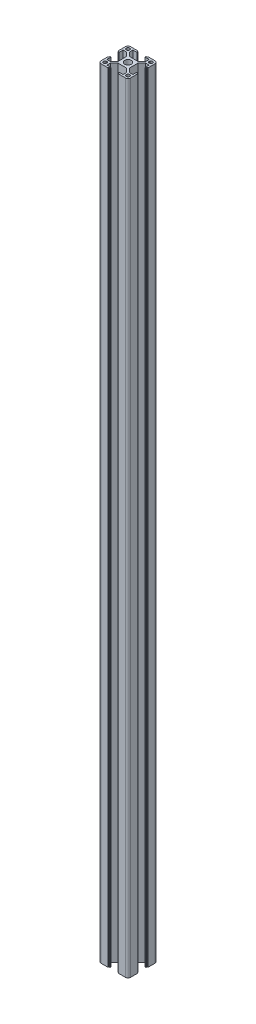
SolidWorks part; units mm, degrees
material "6063-T5"
ref_plane "前视基准面" through (0, 0, 0) normal (0, 0, 1) x (1, 0, 0)
ref_plane "上视基准面" through (0, 0, 0) normal (0, 1, 0) x (1, 0, 0)
ref_plane "右视基准面" through (0, 0, 0) normal (1, 0, 0) x (0, 0, -1)
sketch "草图3" plane through (0, 0, 0) normal (0, 1, 0) x (1, 0, 0)
  line L0 (0, 0) -> (-15, -15) construction
  line L1 (-15, -15) -> (-15, 0) construction
  line L2 (-15, 0) -> (0, 0) construction
  line L3 (-15, -12.5) -> (-15, -5.4)
  line L4 (-14.8, -5.2) -> (-14.4, -5.2)
  line L5 (-14.2, -5) -> (-14.2, -4.3)
  line L6 (-14, -4.1) -> (-13.2, -4.1)
  line L7 (-13.2, -4.1) -> (-13.2, -8.25)
  line L8 (-13.2, -8.25) -> (-9.5228, -8.25)
  line L9 (-9.5228, -8.25) -> (-5.8, -4.5272)
  line L10 (-5.8, -4.5272) -> (-5.8, 4.5272)
  line L11 (-13.2, -12.2) -> (-13.2, -11.05)
  line L12 (-12.2, -10.05) -> (-11.05, -10.05)
  line L13 (-4.5272, -5.8) -> (4.5272, -5.8)
  line L14 (-8.25, -9.5228) -> (-4.5272, -5.8)
  line L15 (-12.2, -13.2) -> (-11.05, -13.2)
  line L16 (-10.05, -12.2) -> (-10.05, -11.05)
  line L17 (-5.2, -14.8) -> (-5.2, -14.4)
  line L18 (-5, -14.2) -> (-4.3, -14.2)
  line L19 (-4.1, -14) -> (-4.1, -13.2)
  line L20 (-4.1, -13.2) -> (-8.25, -13.2)
  line L21 (-8.25, -13.2) -> (-8.25, -9.5228)
  line L22 (-12.5, -15) -> (-5.4, -15)
  line L23 (-12.5, 15) -> (-5.4, 15)
  line L24 (-8.25, 13.2) -> (-8.25, 9.5228)
  line L25 (-4.1, 13.2) -> (-8.25, 13.2)
  line L26 (-4.1, 14) -> (-4.1, 13.2)
  line L27 (-5, 14.2) -> (-4.3, 14.2)
  line L28 (-5.2, 14.8) -> (-5.2, 14.4)
  line L29 (-10.05, 12.2) -> (-10.05, 11.05)
  line L30 (-12.2, 13.2) -> (-11.05, 13.2)
  line L31 (-8.25, 9.5228) -> (-4.5272, 5.8)
  line L32 (-4.5272, 5.8) -> (4.5272, 5.8)
  line L33 (-12.2, 10.05) -> (-11.05, 10.05)
  line L34 (-13.2, 12.2) -> (-13.2, 11.05)
  line L35 (-9.5228, 8.25) -> (-5.8, 4.5272)
  line L36 (-13.2, 8.25) -> (-9.5228, 8.25)
  line L37 (-13.2, 4.1) -> (-13.2, 8.25)
  line L38 (-14, 4.1) -> (-13.2, 4.1)
  line L39 (-14.2, 5) -> (-14.2, 4.3)
  line L40 (-14.8, 5.2) -> (-14.4, 5.2)
  line L41 (-15, 12.5) -> (-15, 5.4)
  line L42 (0, 0) -> (0, -12.3268) construction
  line L43 (15, 12.5) -> (15, 5.4)
  line L44 (14.8, 5.2) -> (14.4, 5.2)
  line L45 (14.2, 5) -> (14.2, 4.3)
  line L46 (14, 4.1) -> (13.2, 4.1)
  line L47 (13.2, 4.1) -> (13.2, 8.25)
  line L48 (13.2, 8.25) -> (9.5228, 8.25)
  line L49 (9.5228, 8.25) -> (5.8, 4.5272)
  line L50 (13.2, 12.2) -> (13.2, 11.05)
  line L51 (12.2, 10.05) -> (11.05, 10.05)
  line L52 (8.25, 9.5228) -> (4.5272, 5.8)
  line L53 (12.2, 13.2) -> (11.05, 13.2)
  line L54 (10.05, 12.2) -> (10.05, 11.05)
  line L55 (5.2, 14.8) -> (5.2, 14.4)
  line L56 (5, 14.2) -> (4.3, 14.2)
  line L57 (4.1, 14) -> (4.1, 13.2)
  line L58 (4.1, 13.2) -> (8.25, 13.2)
  line L59 (8.25, 13.2) -> (8.25, 9.5228)
  line L60 (12.5, 15) -> (5.4, 15)
  line L61 (12.5, -15) -> (5.4, -15)
  line L62 (8.25, -13.2) -> (8.25, -9.5228)
  line L63 (4.1, -13.2) -> (8.25, -13.2)
  line L64 (4.1, -14) -> (4.1, -13.2)
  line L65 (5, -14.2) -> (4.3, -14.2)
  line L66 (5.2, -14.8) -> (5.2, -14.4)
  line L67 (10.05, -12.2) -> (10.05, -11.05)
  line L68 (12.2, -13.2) -> (11.05, -13.2)
  line L69 (8.25, -9.5228) -> (4.5272, -5.8)
  line L70 (12.2, -10.05) -> (11.05, -10.05)
  line L71 (13.2, -12.2) -> (13.2, -11.05)
  line L72 (5.8, -4.5272) -> (5.8, 4.5272)
  line L73 (9.5228, -8.25) -> (5.8, -4.5272)
  line L74 (13.2, -8.25) -> (9.5228, -8.25)
  line L75 (13.2, -4.1) -> (13.2, -8.25)
  line L76 (14, -4.1) -> (13.2, -4.1)
  line L77 (14.2, -5) -> (14.2, -4.3)
  line L78 (14.8, -5.2) -> (14.4, -5.2)
  line L79 (15, -12.5) -> (15, -5.4)
  circle A0 centre (0, 0) radius 3.4
  arc A1 (-12.5, 15) -> (-15, 12.5) centre (-12.5, 12.5) ccw
  arc A2 (15, 12.5) -> (12.5, 15) centre (12.5, 12.5) ccw
  arc A3 (12.5, -15) -> (15, -12.5) centre (12.5, -12.5) ccw
  arc A4 (-15, -12.5) -> (-12.5, -15) centre (-12.5, -12.5) ccw
  arc A5 (-12.2, 13.2) -> (-13.2, 12.2) centre (-12.2, 12.2) ccw
  arc A6 (-12.2, 10.05) -> (-13.2, 11.05) centre (-12.2, 11.05) cw
  arc A7 (-10.05, 11.05) -> (-11.05, 10.05) centre (-11.05, 11.05) cw
  arc A8 (-10.05, 12.2) -> (-11.05, 13.2) centre (-11.05, 12.2) ccw
  arc A9 (11.05, 10.05) -> (10.05, 11.05) centre (11.05, 11.05) cw
  arc A10 (11.05, 13.2) -> (10.05, 12.2) centre (11.05, 12.2) ccw
  arc A11 (13.2, 12.2) -> (12.2, 13.2) centre (12.2, 12.2) ccw
  arc A12 (13.2, 11.05) -> (12.2, 10.05) centre (12.2, 11.05) cw
  arc A13 (12.2, -10.05) -> (13.2, -11.05) centre (12.2, -11.05) cw
  arc A14 (10.05, -11.05) -> (11.05, -10.05) centre (11.05, -11.05) cw
  arc A15 (10.05, -12.2) -> (11.05, -13.2) centre (11.05, -12.2) ccw
  arc A16 (12.2, -13.2) -> (13.2, -12.2) centre (12.2, -12.2) ccw
  arc A17 (-13.2, -11.05) -> (-12.2, -10.05) centre (-12.2, -11.05) cw
  arc A18 (-11.05, -10.05) -> (-10.05, -11.05) centre (-11.05, -11.05) cw
  arc A19 (-11.05, -13.2) -> (-10.05, -12.2) centre (-11.05, -12.2) ccw
  arc A20 (-13.2, -12.2) -> (-12.2, -13.2) centre (-12.2, -12.2) ccw
  arc A21 (-15, -5.4) -> (-14.8, -5.2) centre (-14.8, -5.4) cw
  arc A22 (-14.4, -5.2) -> (-14.2, -5) centre (-14.4, -5) ccw
  arc A23 (-14.2, -4.3) -> (-14, -4.1) centre (-14, -4.3) cw
  arc A24 (-14, 4.1) -> (-14.2, 4.3) centre (-14, 4.3) cw
  arc A25 (-14.2, 5) -> (-14.4, 5.2) centre (-14.4, 5) ccw
  arc A26 (-14.8, 5.2) -> (-15, 5.4) centre (-14.8, 5.4) cw
  arc A27 (-5.4, 15) -> (-5.2, 14.8) centre (-5.4, 14.8) cw
  arc A28 (-5, 14.2) -> (-5.2, 14.4) centre (-5, 14.4) cw
  arc A29 (-4.1, 14) -> (-4.3, 14.2) centre (-4.3, 14) ccw
  arc A30 (5.2, 14.8) -> (5.4, 15) centre (5.4, 14.8) cw
  arc A31 (5.2, 14.4) -> (5, 14.2) centre (5, 14.4) cw
  arc A32 (4.3, 14.2) -> (4.1, 14) centre (4.3, 14) ccw
  arc A33 (15, 5.4) -> (14.8, 5.2) centre (14.8, 5.4) cw
  arc A34 (14.4, 5.2) -> (14.2, 5) centre (14.4, 5) ccw
  arc A35 (14.2, 4.3) -> (14, 4.1) centre (14, 4.3) cw
  arc A36 (14, -4.1) -> (14.2, -4.3) centre (14, -4.3) cw
  arc A37 (14.2, -5) -> (14.4, -5.2) centre (14.4, -5) ccw
  arc A38 (14.8, -5.2) -> (15, -5.4) centre (14.8, -5.4) cw
  arc A39 (5.4, -15) -> (5.2, -14.8) centre (5.4, -14.8) cw
  arc A40 (5, -14.2) -> (5.2, -14.4) centre (5, -14.4) cw
  arc A41 (4.1, -14) -> (4.3, -14.2) centre (4.3, -14) ccw
  arc A42 (-5.2, -14.4) -> (-5, -14.2) centre (-5, -14.4) cw
  arc A43 (-4.3, -14.2) -> (-4.1, -14) centre (-4.3, -14) ccw
  arc A44 (-5.2, -14.8) -> (-5.4, -15) centre (-5.4, -14.8) cw
  point P38 (-5.8, 0)
  point P46 (0, 5.8)
  point P47 (0, -5.8)
  point P83 (5.8, 0)
  point P87 (-15, 15)
  point P90 (15, 15)
  point P93 (15, -15)
  point P99 (-13.2, 13.2)
  point P102 (-13.2, 10.05)
  point P105 (-10.05, 10.05)
  point P108 (-10.05, 13.2)
  point P111 (10.05, 10.05)
  point P114 (10.05, 13.2)
  point P117 (13.2, 13.2)
  point P120 (13.2, 10.05)
  point P123 (13.2, -10.05)
  point P126 (10.05, -10.05)
  point P129 (10.05, -13.2)
  point P132 (13.2, -13.2)
  point P135 (-13.2, -10.05)
  point P138 (-10.05, -10.05)
  point P141 (-10.05, -13.2)
  point P144 (-13.2, -13.2)
  point P147 (-15, -5.2)
  point P150 (-14.2, -5.2)
  point P153 (-14.2, -4.1)
  point P156 (-14.2, 4.1)
  point P159 (-14.2, 5.2)
  point P162 (-15, 5.2)
  point P165 (-5.2, 15)
  point P168 (-5.2, 14.2)
  point P171 (-4.1, 14.2)
  point P174 (5.2, 15)
  point P177 (5.2, 14.2)
  point P180 (4.1, 14.2)
  point P183 (15, 5.2)
  point P186 (14.2, 5.2)
  point P189 (14.2, 4.1)
  point P192 (14.2, -4.1)
  point P195 (14.2, -5.2)
  point P198 (15, -5.2)
  point P201 (5.2, -15)
  point P204 (5.2, -14.2)
  point P207 (4.1, -14.2)
  point P210 (-5.2, -14.2)
  point P213 (-4.1, -14.2)
  point P216 (-5.2, -15)
  dimension "D11" = 6.8
  dimension "D12" = 2.5
  dimension "D13" = 1
  dimension "D14" = 0.2
  dimension "D2" = 15
  dimension "D3" = 4.1
  dimension "D4" = 5.2
  dimension "D5" = 0.8
  dimension "D6" = 1.8
  dimension "D7" = 9.2
  dimension "D8" = 8.25
  dimension "D9" = 0.9
  dimension "D10" = 1.8
extrude "凸台-拉伸1" add sketch "草图3" along normal blind 789
ref_plane "基准面1" through (-10.05, 394.5, 12.2) normal (0, -1, 0) x (-1, 0, 0)
sketch "草图4" plane through (0, 0, 5.8) normal (0, 0, 1) x (1, 0, 0)
  line L1 (-4.5272, 789) -> (4.5272, 789) construction
  line L2 (5.4, 0) -> (12.5, 0) construction
  circle A1 centre (0, 609) radius 3
  circle A2 centre (0, 180) radius 3
  circle A4 centre (0, 394.5) radius 3
  point P2 (0, 386.1803)
  dimension "D1" = 6
  dimension "D2" = 6
  dimension "D3" = 6
  dimension "D4" = 180
  dimension "D5" = 180
  dimension "D6" = 394.5
extrude "切除-拉伸1" cut sketch "草图4" against normal blind 86
